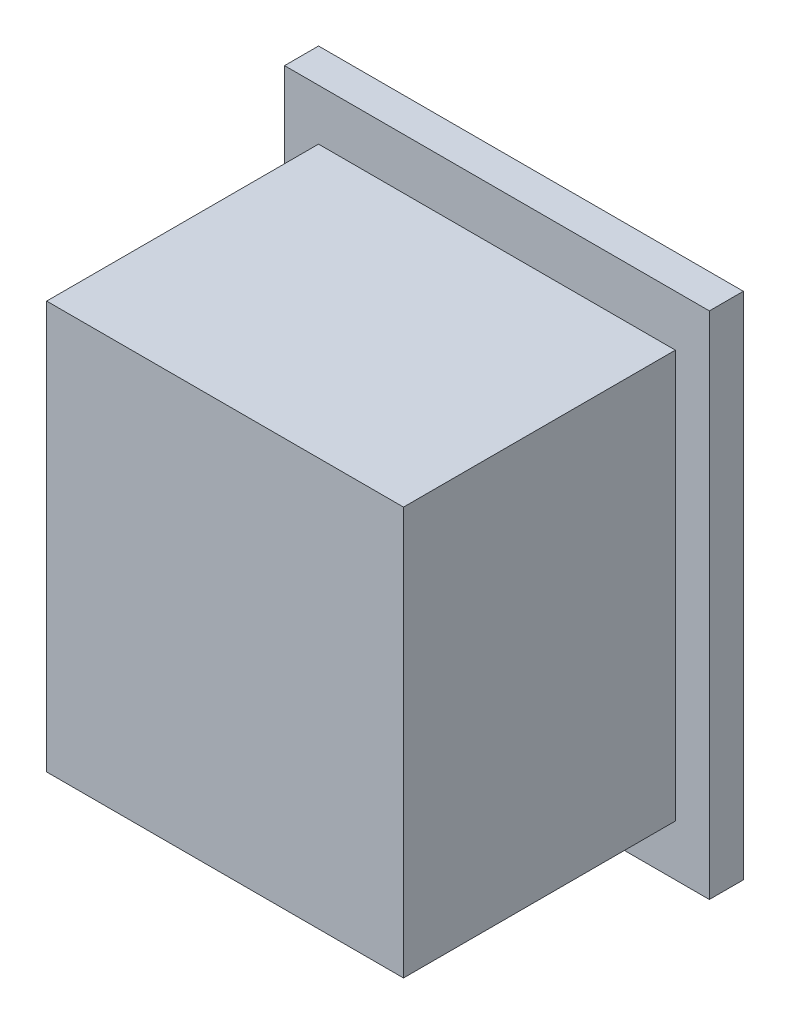
SolidWorks part; units mm, degrees
ref_plane "Front Plane" through (0, 0, 0) normal (0, 0, 1) x (1, 0, 0)
ref_plane "Top Plane" through (0, 0, 0) normal (0, 1, 0) x (1, 0, 0)
ref_plane "Right Plane" through (0, 0, 0) normal (1, 0, 0) x (0, 0, -1)
sketch "Sketch1" plane through (0, 0, 0) normal (0, 0, 1) x (1, 0, 0)
  line L1 (-12.5825, 13.165) -> (8.4175, 13.165)
  line L2 (-12.5825, 13.165) -> (-12.5825, -10.835)
  line L3 (-12.5825, -10.835) -> (8.4175, -10.835)
  line L4 (8.4175, 13.165) -> (8.4175, -10.835)
  dimension "D1" = 24
  dimension "D2" = 21
extrude "Boss-Extrude1" add sketch "Sketch1" along normal blind 16
sketch "Sketch2" plane through (0, 0, 0) normal (0, 0, -1) x (-1, 0, 0)
  line L0 (14.5825, 16.165) -> (-10.4175, 16.165)
  line L1 (-10.4175, 16.165) -> (-10.4175, -13.835)
  line L2 (-10.4175, -13.835) -> (14.5825, -13.835)
  line L3 (14.5825, -13.835) -> (14.5825, 16.165)
  line L4 (-8.4175, -10.835) -> (-8.4175, 13.165) construction
  line L5 (12.5825, 13.165) -> (12.5825, -10.835) construction
  line L6 (-8.4175, 13.165) -> (12.5825, 13.165) construction
  line L7 (12.5825, -10.835) -> (-8.4175, -10.835) construction
  dimension "D1" = 2
  dimension "D2" = 2
  dimension "D3" = 3
  dimension "D4" = 3
extrude "Boss-Extrude2" add sketch "Sketch2" along normal blind 2
